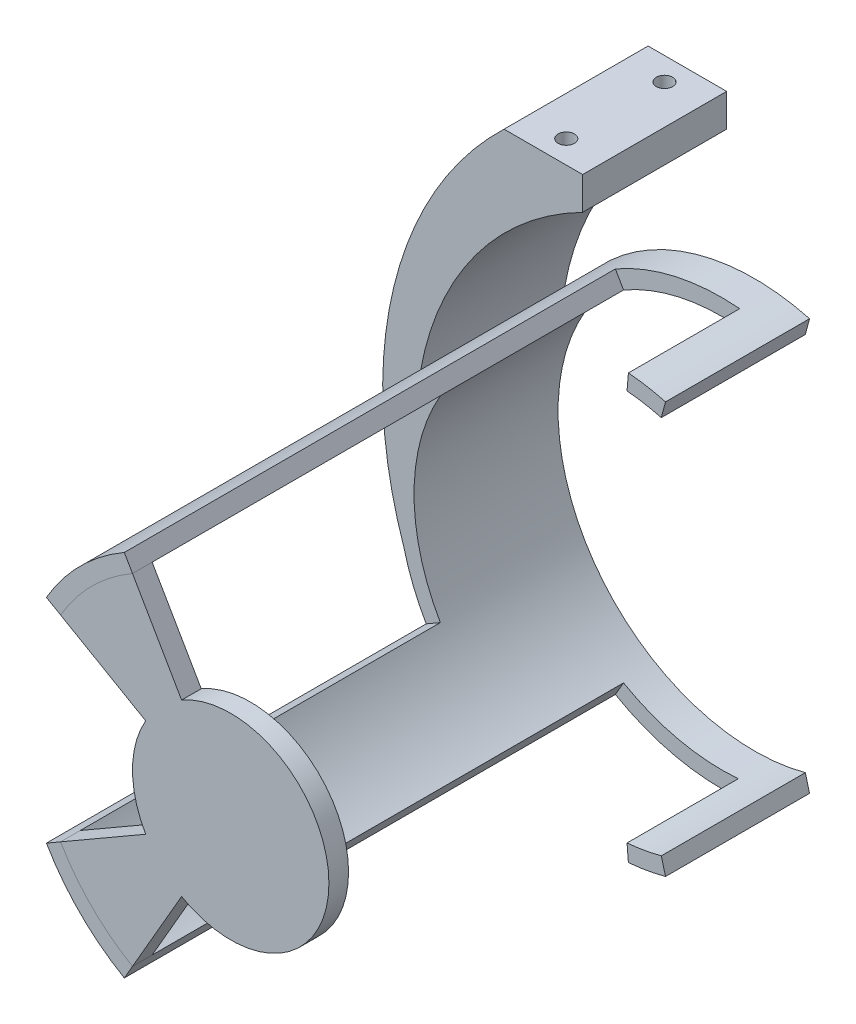
SolidWorks part; units mm, degrees
ref_plane "Plan de face" through (0, 0, 0) normal (0, 0, 1) x (1, 0, 0)
ref_plane "Plan de dessus" through (0, 0, 0) normal (0, 1, 0) x (1, 0, 0)
ref_plane "Plan de droite" through (0, 0, 0) normal (1, 0, 0) x (0, 0, -1)
sketch "Esquisse1" plane through (0, 0, 0) normal (0, 0, 1) x (1, 0, 0)
  circle A0 centre (0, 0) radius 30
  circle A1 centre (0, 0) radius 32.5
  dimension "D2" = 60
  dimension "D1" = 2.5
extrude "Boss.-Extru.1" add sketch "Esquisse1" along normal blind 22
sketch "Esquisse2" plane through (0, 0, 22) normal (0, 0, 1) x (1, 0, 0)
  line L0 (-16.25, 28.1458) -> (-15, 25.9808)
  line L1 (-28.1458, 16.25) -> (-25.9808, 15)
  line L2 (55, 0) -> (-55, 0) construction
  line L3 (-28.1458, -16.25) -> (-25.9808, -15)
  line L4 (-16.25, -28.1458) -> (-15, -25.9808)
  arc A0 (-16.25, 28.1458) -> (-28.1458, 16.25) centre (0, 0) ccw
  circle A1 centre (0, 0) radius 32.5 construction
  arc A2 (-15, 25.9808) -> (-25.9808, 15) centre (0, 0) ccw
  arc A3 (-16.25, -28.1458) -> (-28.1458, -16.25) centre (0, 0) cw
  arc A4 (-15, -25.9808) -> (-25.9808, -15) centre (0, 0) cw
  dimension "D1" = 30
extrude "Boss.-Extru.2" add sketch "Esquisse2" along normal blind 58
sketch "Esquisse3" plane through (0, 0, 0) normal (0, 0, -1) x (-1, 0, 0)
  line L0 (12.9904, 7.5) -> (25.9808, 15)
  line L1 (7.5, 12.9904) -> (15, 25.9808)
  line L2 (12.1, 0) -> (-12.1, 0) construction
  line L3 (12.9904, -7.5) -> (25.9808, -15)
  line L4 (7.5, -12.9904) -> (15, -25.9808)
  arc A0 (7.5, 12.9904) -> (7.5, -12.9904) centre (0, 0) ccw
  arc A1 (12.9904, 7.5) -> (12.9904, -7.5) centre (0, 0) cw
  circle A2 centre (0, 0) radius 30 construction
  arc A3 (25.9808, -15) -> (14.9151, -26.0296) centre (0, 0) cw
  arc A4 (25.9808, 15) -> (15, 25.9808) centre (0, 0) ccw
  circle M6 centre (0, 0) radius 30
  dimension "D1" = 15
  dimension "D2" = 15
  dimension "D3" = 30
  dimension "D4" = 60
extrude "Boss.-Extru.3" add sketch "Esquisse3" along direction (0, 0, 1) on the side against the normal blind 3 from offset 77 separate body contours A1 L0 L1 A0 L4 L3 M6 offset against normal yes
sketch "Esquisse5" plane through (0, 0, 0) normal (0, 0, -1) x (-1, 0, 0)
  line L0 (4.25, 50.1317) -> (4.25, 55.1317)
  line L1 (4.25, 55.1317) -> (16.25, 55.1317)
  arc A0 (31.5234, -7.9075) -> (29.4553, 13.7344) centre (0, 0) ccw
  circle A1 centre (0, 0) radius 32.5 construction
  arc A2 (29.4553, 13.7344) -> (4.25, 50.1317) centre (-16.9211, 8.5446) ccw
  arc A3 (31.5234, -7.9075) -> (16.25, 55.1317) centre (-25.4463, 11.6596) ccw
  dimension "D1" = 5
  dimension "D2" = 12
extrude "Boss.-Extru.4" add sketch "Esquisse5" against normal blind 22
sketch "Esquisse6" plane through (0, 0, 0) normal (0, 0, -1) x (-1, 0, 0)
  line L0 (0, 0) -> (-10.2628, -38.3014)
  line L1 (-10.2628, -38.3014) -> (-52.3208, 0)
  line L2 (37.0095, 0) -> (-37.0095, 0) construction
  line L3 (-10.2628, 38.3014) -> (-52.3208, 0)
  line L4 (0, 0) -> (-10.2628, 38.3014)
  dimension "D1" = 150
extrude "Enlèv. mat.-Extru.1" cut sketch "Esquisse6" against normal blind 22
sketch "Esquisse8" plane through (0, 0, 0) normal (0, 0, -1) x (-1, 0, 0)
  line L0 (-2.7408, 32.3842) -> (-1.5219, 17.9819)
  line L1 (16.25, 28.1458) -> (8.3801, 14.5147)
  line L2 (8.3801, 14.5147) -> (-1.5219, 17.9819)
  line L3 (27.3845, 0) -> (-27.3845, 0) construction
  line L4 (-2.7408, -32.3842) -> (-1.5219, -17.9819)
  line L5 (8.3801, -14.5147) -> (-1.5219, -17.9819)
  line L6 (16.25, -28.1458) -> (8.3801, -14.5147)
  arc A0 (16.25, 28.1458) -> (-2.7408, 32.3842) centre (0, 0) ccw
  arc A1 (29.4553, 13.7344) -> (-8.4116, 31.3926) centre (0, 0) ccw construction
  arc A2 (16.25, -28.1458) -> (-2.7408, -32.3842) centre (0, 0) cw
  dimension "D1" = 120
extrude "Enlèv. mat.-Extru.3" cut sketch "Esquisse8" against normal blind 52 from offset 5 offset against normal yes
sketch "Esquisse9" plane through (0, 55.1317, 0) normal (0, 1, 0) x (1, 0, 0)
  line L0 (-10.25, 0) -> (-10.25, -3.5) construction
  line L1 (-16.25, 0) -> (-4.25, 0) construction
  line L2 (-10.25, -22) -> (-10.25, -18.5) construction
  line L3 (-16.25, -22) -> (-4.25, -22) construction
  circle A0 centre (-10.25, -3.5) radius 1.25
  circle A1 centre (-10.25, -18.5) radius 1.25
  dimension "D3" = 2.5
  dimension "D4" = 2.5
  dimension "D1" = 3.5
  dimension "D2" = 3.5
extrude "Enlèv. mat.-Extru.4" cut sketch "Esquisse9" against normal blind 4
sketch "Esquisse10" plane through (0, 51.1317, 0) normal (0, 1, 0) x (1, 0, 0)
  circle A0 centre (-10.25, -3.5) radius 2.5
  circle A1 centre (-10.25, -18.5) radius 2.5
  dimension "D1" = 5
  dimension "D2" = 5
extrude "Enlèv. mat.-Extru.5" cut sketch "Esquisse10" against normal up to next
